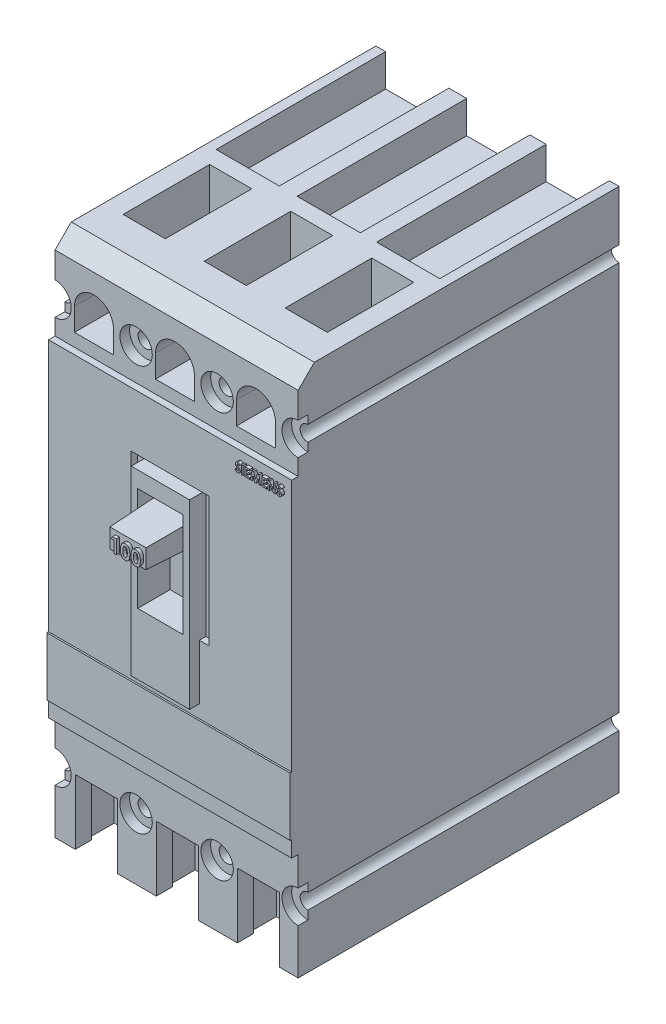
SolidWorks part; units mm, degrees
ref_plane "Alzado" through (0, 0, 0) normal (0, 0, 1) x (1, 0, 0)
ref_plane "Planta" through (0, 0, 0) normal (0, 1, 0) x (1, 0, 0)
ref_plane "Vista lateral" through (0, 0, 0) normal (1, 0, 0) x (0, 0, -1)
sketch "Croquis1" plane through (0, 0, 0) normal (0, 0, 1) x (1, 0, 0)
  line L1 (-37.5, -81) -> (37.5, -81)
  line L2 (-37.5, -81) -> (-37.5, 81)
  line L3 (-37.5, 81) -> (37.5, 81)
  line L4 (37.5, -81) -> (37.5, 81)
  line L5 (-37.5, -81) -> (37.5, 81) construction
  line L6 (-37.5, 81) -> (37.5, -81) construction
  point P0 (0, 0)
  dimension "D1" = 75
  dimension "D2" = 162
extrude "Saliente-Extruir1" add sketch "Croquis1" along normal blind 101
sketch "Croquis2" plane through (0, 0, 101) normal (0, 0, 1) x (1, 0, 0)
  line L0 (-37.5, -48) -> (37.5, -48)
  line L1 (-37.5, 81) -> (-37.5, -81) construction
  line L2 (37.5, -81) -> (37.5, 81) construction
  line L3 (-37.5, -81) -> (37.5, -81) construction
  line L4 (-37.5, 53) -> (37.5, 53)
  line L5 (37.5, 53) -> (37.5, 81)
  line L6 (37.5, 81) -> (-37.5, 81)
  line L7 (-37.5, 81) -> (-37.5, 53)
  line L8 (-37.5, -48) -> (-37.5, -81)
  line L9 (-37.5, -81) -> (37.5, -81)
  line L10 (37.5, -81) -> (37.5, -48)
  dimension "D1" = 33
  dimension "D2" = 101
extrude "Cortar-Extruir1" cut sketch "Croquis2" against normal blind 2
sketch "Croquis3" plane through (0, 0, 99) normal (0, 0, 1) x (1, 0, 0)
  line L0 (-31.5, 57) -> (-19.5, 57)
  line L1 (-19.5, 57) -> (-19.5, 64)
  line L2 (-37.5, 53) -> (37.5, 53) construction
  line L3 (-37.5, 81) -> (-37.5, 53) construction
  line L4 (-31.5, 57) -> (-31.5, 64)
  line L5 (-6.5, 57) -> (-6.5, 64)
  line L6 (-6.5, 57) -> (5.5, 57)
  line L7 (5.5, 57) -> (5.5, 64)
  line L8 (18.5, 57) -> (18.5, 64)
  line L9 (18.5, 57) -> (30.5, 57)
  line L10 (30.5, 57) -> (30.5, 64)
  arc A0 (-31.5, 64) -> (-19.5, 64) centre (-25.5, 64) cw
  arc A1 (-6.5, 64) -> (5.5, 64) centre (-0.5, 64) cw
  arc A2 (18.5, 64) -> (30.5, 64) centre (24.5, 64) cw
  dimension "D1" = 4
  dimension "D2" = 6
  dimension "D3" = 7
  dimension "D4" = 12
  dimension "D5" = 13
  dimension "D6" = 12
  dimension "D7" = 13
  dimension "D8" = 12
extrude "Cortar-Extruir2" cut sketch "Croquis3" against normal blind 15
sketch "Croquis4" plane through (0, 0, 99) normal (0, 0, 1) x (1, 0, 0)
  line L0 (-31.25, -81) -> (-31.25, -61)
  line L1 (-37.5, -81) -> (37.5, -81) construction
  line L2 (-31.25, -61) -> (-18.25, -61)
  line L3 (-18.25, -61) -> (-18.25, -81)
  line L4 (-18.25, -81) -> (-31.25, -81)
  line L5 (-37.5, -48) -> (-37.5, -81) construction
  line L6 (-6.25, -81) -> (-6.25, -61)
  line L7 (-6.25, -61) -> (6.75, -61)
  line L8 (6.75, -61) -> (6.75, -81)
  line L9 (6.75, -81) -> (-6.25, -81)
  line L10 (6.75, -81) -> (-6.25, -81)
  line L11 (18.75, -81) -> (18.75, -61)
  line L12 (18.75, -61) -> (31.75, -61)
  line L13 (31.75, -61) -> (31.75, -81)
  line L14 (31.75, -81) -> (18.75, -81)
  line L15 (18.75, -81) -> (31.75, -81)
  line M10 (-37.5, -81) -> (37.5, -81)
  dimension "D1" = 6.25
  dimension "D2" = 20
  dimension "D3" = 13
  dimension "D4" = 12
  dimension "D5" = 13
  dimension "D6" = 12
  dimension "D7" = 13
extrude "Cortar-Extruir3" cut sketch "Croquis4" against normal blind 5 contours L8 L7 L6 M10 | L3 L2 L0 M10 | L13 L12 L11 M10
sketch "Croquis5" plane through (0, 0, 99) normal (0, 0, 1) x (1, 0, 0)
  line L0 (-37.5, 81) -> (-37.5, 53) construction
  line L1 (37.5, 53) -> (37.5, 81) construction
  line L2 (-37.5, 53) -> (37.5, 53) construction
  line L3 (-37.5, 53) -> (37.5, 53) construction
  circle A0 centre (-12.5, 63) radius 5
  circle A1 centre (12.5, 63) radius 5
  dimension "D3" = 10
  dimension "D5" = 10
  dimension "D6" = 10
  dimension "D1" = 25
  dimension "D2" = 25
  dimension "D4" = 10
extrude "Cortar-Extruir4" cut sketch "Croquis5" against normal blind 3
sketch "Croquis6" plane through (0, 0, 99) normal (0, 0, 1) x (1, 0, 0)
  line L0 (-37.5, 81) -> (-37.5, 53) construction
  line L1 (37.5, 53) -> (37.5, 81) construction
  circle A0 centre (-37.5, 63) radius 5
  circle A1 centre (37.5, 63) radius 5
  dimension "D1" = 10
  dimension "D2" = 10
extrude "Cortar-Extruir5" cut sketch "Croquis6" against normal blind 3
sketch "Croquis7" plane through (0, 0, 96) normal (0, 0, 1) x (1, 0, 0)
  line L0 (37.5, 58) -> (37.5, 68) construction
  line L1 (-37.5, 68) -> (-37.5, 58) construction
  circle A0 centre (37.5, 63) radius 2.3812
  circle A1 centre (12.5, 63) radius 2.38
  circle A2 centre (-37.5, 63) radius 2.3812
  circle A3 centre (-12.5, 63) radius 2.38
  dimension "D1" = 4.7625
  dimension "D2" = 4.7625
  dimension "D3" = 4.76
  dimension "D4" = 4.76
extrude "Cortar-Extruir6" cut sketch "Croquis7" against normal up to surface (96 mm away) up to face at (0, 0, 0)
sketch "Croquis8" plane through (0, 0, 99) normal (0, 0, 1) x (1, 0, 0)
  line L0 (37.5, -81) -> (37.5, -48) construction
  line L1 (-37.5, -48) -> (-37.5, -81) construction
  line L2 (37.5, -48) -> (-37.5, -48) construction
  line L3 (37.5, -48) -> (-37.5, -48) construction
  circle A0 centre (-12.5, -62) radius 5
  circle A1 centre (12.5, -62) radius 5
  circle A2 centre (37.5, -62) radius 5
  circle A3 centre (-37.5, -62) radius 5
  dimension "D1" = 10
  dimension "D2" = 10
  dimension "D3" = 10
  dimension "D4" = 10
  dimension "D8" = 14
  dimension "D9" = 14
  dimension "D10" = 14
  dimension "D5" = 25
  dimension "D6" = 25
  dimension "D7" = 14
extrude "Cortar-Extruir7" cut sketch "Croquis8" against normal blind 3
sketch "Croquis9" plane through (0, 0, 96) normal (0, 0, 1) x (1, 0, 0)
  line L0 (-37.5, -57) -> (-37.5, -67) construction
  line L1 (37.5, -67) -> (37.5, -57) construction
  circle A0 centre (-37.5, -62) radius 2.38
  circle A1 centre (-12.5, -62) radius 2.38
  circle A2 centre (37.5, -62) radius 2.38
  circle A3 centre (12.5, -62) radius 2.38
  dimension "D1" = 4.76
  dimension "D2" = 4.76
  dimension "D3" = 4.76
  dimension "D4" = 4.76
extrude "Cortar-Extruir8" cut sketch "Croquis9" against normal up to surface (96 mm away) up to face at (10.12, 63, 0)
sketch "Croquis10" plane through (0, 81, 0) normal (0, 1, 0) x (1, 0, 0)
  line L0 (-31.5, -84) -> (-31.5, -57.3047)
  line L1 (-31.5, -57.3047) -> (-18.5, -57.3047)
  line L2 (-18.5, -57.3047) -> (-18.5, -84)
  line L3 (-18.5, -84) -> (-31.5, -84)
  line L4 (-37.5, -99) -> (-37.5, 0) construction
  line L5 (-37.5, -99) -> (37.5, -99) construction
  line L6 (-6.5, -84) -> (-6.5, -57.3047)
  line L7 (-6.5, -57.3047) -> (6.5, -57.3047)
  line L8 (6.5, -57.3047) -> (6.5, -84)
  line L9 (6.5, -84) -> (-6.5, -84)
  line L10 (18.5, -84) -> (18.5, -57.3047)
  line L11 (18.5, -57.3047) -> (31.5, -57.3047)
  line L12 (31.5, -57.3047) -> (31.5, -84)
  line L13 (31.5, -84) -> (18.5, -84)
  dimension "D1" = 6
  dimension "D2" = 15
  dimension "D3" = 13
  dimension "D4" = 12
  dimension "D5" = 13
  dimension "D6" = 12
  dimension "D7" = 13
extrude "Cortar-Extruir9" cut sketch "Croquis10" against normal blind 22
sketch "Croquis11" plane through (0, 81, 0) normal (0, 1, 0) x (1, 0, 0)
  line L0 (-34.5, 0) -> (-34.5, -52.3047)
  line L1 (-34.5, -52.3047) -> (-15, -52.3047)
  line L2 (-15, -52.3047) -> (-15, 0)
  line L3 (-37.5, -99) -> (-37.5, 0) construction
  line L4 (-18.5, -57.3047) -> (-31.5, -57.3047) construction
  line L5 (37.5, 0) -> (-37.5, 0) construction
  line L6 (-34.5, 0) -> (-15, 0)
  line L7 (-9.5, -52.3047) -> (-9.5, 0)
  line L8 (-9.5, -52.3047) -> (10, -52.3047)
  line L9 (10, -52.3047) -> (10, 0)
  line L10 (-9.5, 0) -> (10, 0)
  line L11 (15, -52.3047) -> (15, 0)
  line L12 (15, 0) -> (34.5, 0)
  line L13 (34.5, 0) -> (34.5, -52.3047)
  line L14 (34.5, -52.3047) -> (15, -52.3047)
  dimension "D1" = 3
  dimension "D2" = 5
  dimension "D3" = 19.5
  dimension "D4" = 5.5
  dimension "D5" = 19.5
  dimension "D6" = 5
  dimension "D7" = 19.5
extrude "Cortar-Extruir10" cut sketch "Croquis11" against normal blind 10
sketch "Croquis12" plane through (-37.5, 0, 0) normal (-1, 0, 0) x (0, 0, 1)
  line L0 (99, 81) -> (94, 81)
  line L1 (99, 81) -> (0, 81) construction
  line L2 (99, 81) -> (99, 76)
  line L3 (99, 81) -> (99, 68) construction
  line L4 (99, 76) -> (94, 81)
  dimension "D1" = 5
  dimension "D2" = 5
extrude "Cortar-Extruir11" cut sketch "Croquis12" against normal up to surface (75 mm away) up to face at (37.5, 71.4604, 65)
sketch "Croquis13" plane through (0, -81, 0) normal (0, -1, 0) x (1, 0, 0)
  line L0 (-18.25, 94) -> (-17.25, 94)
  line L1 (-17.25, 94) -> (-17.25, 86)
  line L2 (-17.25, 86) -> (-32.25, 86)
  line L3 (-32.25, 86) -> (-32.25, 94)
  line L4 (-32.25, 94) -> (-31.25, 94)
  line L5 (-31.25, 94) -> (-18.25, 94)
  line L6 (-6.25, 94) -> (-7.25, 94)
  line L7 (-7.25, 94) -> (-7.25, 86)
  line L8 (-7.25, 86) -> (7.75, 86)
  line L9 (7.75, 86) -> (7.75, 94)
  line L10 (7.75, 94) -> (6.75, 94)
  line L11 (6.75, 94) -> (-6.25, 94)
  line L12 (18.75, 94) -> (17.75, 94)
  line L13 (17.75, 94) -> (17.75, 86)
  line L14 (17.75, 86) -> (32.75, 86)
  line L15 (32.75, 86) -> (32.75, 94)
  line L16 (32.75, 94) -> (31.75, 94)
  line L17 (31.75, 94) -> (18.75, 94)
  dimension "D1" = 1
  dimension "D2" = 1
  dimension "D3" = 8
  dimension "D4" = 1
  dimension "D5" = 1
  dimension "D6" = 1
  dimension "D7" = 1
extrude "Cortar-Extruir12" cut sketch "Croquis13" against normal up to surface (20 mm away) up to face at (25.25, -61, 96.5)
sketch "Croquis14" plane through (0, -81, 0) normal (0, -1, 0) x (1, 0, 0)
  line L0 (-30.5, 77) -> (-18.5, 77)
  line L1 (-18.5, 77) -> (-18.5, 64)
  line L2 (-18.5, 64) -> (-30.5, 64)
  line L3 (-30.5, 64) -> (-30.5, 77)
  line L4 (-37.5, 99) -> (-37.5, 0) construction
  line L5 (-32.25, 86) -> (-17.25, 86) construction
  line L6 (-6, 77) -> (-6, 64)
  line L7 (-6, 64) -> (6, 64)
  line L8 (6, 64) -> (6, 77)
  line L9 (6, 77) -> (-6, 77)
  line L10 (18, 77) -> (18, 64)
  line L11 (18, 64) -> (30, 64)
  line L12 (30, 64) -> (30, 77)
  line L13 (30, 77) -> (18, 77)
  dimension "D1" = 7
  dimension "D2" = 9
  dimension "D3" = 13
  dimension "D4" = 12
  dimension "D5" = 12.5
  dimension "D6" = 12
  dimension "D7" = 12
  dimension "D8" = 12
extrude "Cortar-Extruir13" cut sketch "Croquis14" against normal blind 20
sketch "Croquis15" plane through (0, -81, 0) normal (0, -1, 0) x (1, 0, 0)
  line L0 (-34.5, 59) -> (-15, 59)
  line L1 (-15, 59) -> (-15, 28.6103)
  line L2 (-16.6103, 27) -> (-32.9974, 27)
  line L3 (-34.5, 28.9932) -> (-34.5, 59)
  line L4 (-37.5, 99) -> (-37.5, 0) construction
  line L5 (-30.5, 64) -> (-18.5, 64) construction
  line L6 (-10, 59) -> (-10, 28.6103)
  line L7 (-8.3897, 27) -> (7.8897, 27)
  line L8 (9.5, 28.6103) -> (9.5, 59)
  line L9 (9.5, 59) -> (-10, 59)
  line L10 (14.5, 59) -> (14.5, 28.6103)
  line L11 (16.1103, 27) -> (31.8897, 27)
  line L12 (33.5, 28.6103) -> (33.5, 59)
  line L13 (33.5, 59) -> (14.5, 59)
  line L14 (18, 64) -> (30, 64) construction
  line L15 (-34.5, 28.9932) -> (-32.9974, 27)
  line L16 (-15, 28.6103) -> (-16.6103, 27)
  line L17 (-10, 28.6103) -> (-8.3897, 27)
  line L18 (9.5, 28.6103) -> (7.8897, 27)
  line L19 (14.5, 28.6103) -> (16.1103, 27)
  line L20 (33.5, 28.6103) -> (31.8897, 27)
  dimension "D1" = 19.5
  dimension "D2" = 3
  dimension "D3" = 5
  dimension "D4" = 19.5
  dimension "D6" = 5
  dimension "D7" = 5
  dimension "D11" = 5
extrude "Cortar-Extruir14" cut sketch "Croquis15" against normal blind 10
sketch "Croquis16" plane through (0, 0, 101) normal (0, 0, 1) x (1, 0, 0)
  line L0 (-12, 36) -> (12, 36)
  line L1 (-37.5, 53) -> (37.5, 53) construction
  line L2 (-12, 36) -> (-12, -4)
  line L3 (-12, -4) -> (12, -4)
  line L4 (12, -4) -> (12, 36)
  line L5 (-37.5, 53) -> (-37.5, -48) construction
  point P8 (0, 36)
  dimension "D1" = 24
  dimension "D2" = 17
  dimension "D3" = 40
  dimension "D4" = 37.5
extrude "Cortar-Extruir15" cut sketch "Croquis16" against normal blind 2
sketch "Croquis17" plane through (0, 0, 99) normal (0, 0, 1) x (1, 0, 0)
  line L0 (-9, 35) -> (9, 35)
  line L1 (12, 36) -> (-12, 36) construction
  line L2 (12, -4) -> (12, 36) construction
  line L3 (-12, 36) -> (-12, -4) construction
  line L4 (-9, 35) -> (-9, -21)
  line L5 (-9, -21) -> (9, -21)
  line L6 (9, -21) -> (9, 35)
  dimension "D1" = 1
  dimension "D2" = 3
  dimension "D3" = 3
  dimension "D4" = 56
extrude "Saliente-Extruir3" add sketch "Croquis17" along normal blind 5
sketch "Croquis18" plane through (0, 0, 104) normal (0, 0, 1) x (1, 0, 0)
  line L0 (-7, 30) -> (7, 30)
  line L1 (7, 30) -> (7, -2)
  line L2 (7, -2) -> (-7, -2)
  line L3 (-7, -2) -> (-7, 30)
  line L4 (9, -21) -> (9, 35) construction
  line L5 (-9, 35) -> (-9, -21) construction
  line L6 (9, 35) -> (-9, 35) construction
  line L7 (9, -4) -> (12, -4) construction
  dimension "D1" = 2
  dimension "D2" = 2
  dimension "D3" = 5
  dimension "D4" = 2
extrude "Cortar-Extruir17" cut sketch "Croquis18" against normal blind 10
sketch "Croquis19" plane through (0, 0, 94) normal (0, 0, 1) x (1, 0, 0)
  line L1 (-6.2741, 18.8945) -> (6.2741, 18.8945)
  line L2 (-6.2741, 18.8945) -> (-6.2741, 26.1771)
  line L3 (-6.2741, 26.1771) -> (6.2741, 26.1771)
  line L4 (6.2741, 18.8945) -> (6.2741, 26.1771)
  line L5 (-6.2741, 18.8945) -> (6.2741, 26.1771) construction
  line L6 (-6.2741, 26.1771) -> (6.2741, 18.8945) construction
  point P0 (0, 22.5358)
extrude "Saliente-Extruir4" add sketch "Croquis19" along normal blind 20 draft 2
sketch "Croquis20" plane through (0, 0, 114) normal (0, 0, 1) x (1, 0, 0)
  line L0 (-4.7336, 20.0134) -> (4.8971, 20.0134) construction
  text T0 "100" font "Century Gothic" height in points 16
extrude "Saliente-Extruir5" add sketch "Croquis20" along normal blind 1
sketch "Croquis21" plane through (0, 0, 101) normal (0, 0, 1) x (1, 0, 0)
  line L0 (20.9057, 47.7503) -> (36.4053, 47.7503) construction
  text T0 "SIEMENS" font "Century Gothic" height in points 10
extrude "Saliente-Extruir6" add sketch "Croquis21" along normal blind 1
sketch "Croquis22" plane through (0, 0, 101) normal (0, 0, 1) x (1, 0, 0)
  line L0 (-37.5, -43) -> (37.5, -43)
  line L1 (-37.5, 53) -> (-37.5, -48) construction
  line L2 (37.5, -48) -> (37.5, 53) construction
  line L3 (37.5, -48) -> (-37.5, -48) construction
  line L4 (-37.5, -25) -> (37.5, -25)
  line L5 (-37.5, -43) -> (-37.5, -25)
  line L6 (37.5, -43) -> (37.5, -25)
  dimension "D1" = 5
  dimension "D2" = 18
extrude "Saliente-Extruir7" add sketch "Croquis22" along normal blind 0.5
